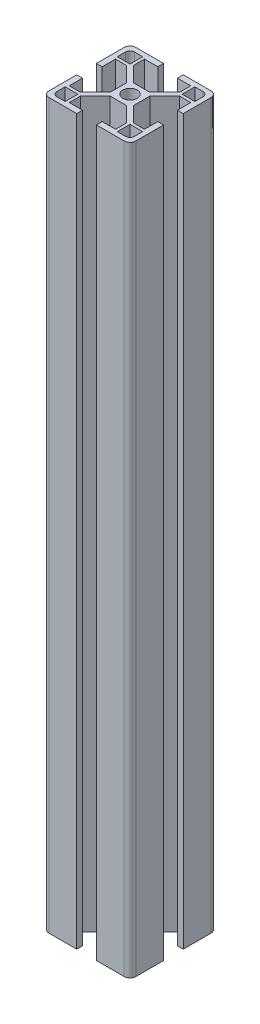
SolidWorks part; units mm, degrees
ref_plane "Front Plane" through (0, 0, 0) normal (0, 0, 1) x (1, 0, 0)
ref_plane "Top Plane" through (0, 0, 0) normal (0, 1, 0) x (1, 0, 0)
ref_plane "Right Plane" through (0, 0, 0) normal (1, 0, 0) x (0, 0, -1)
sketch "Sketch1" plane through (0, 0, 0) normal (0, 1, 0) x (1, 0, 0)
  line L0 (0, 15) -> (30, 15) construction
  line L1 (0, 28) -> (0, 18.4)
  line L2 (30, 28) -> (30, 18.4)
  line L3 (2, 30) -> (11.6, 30)
  line L4 (28, 30) -> (18.4, 30)
  line L5 (15, 0) -> (15, 30) construction
  line L6 (30, 0) -> (11, 19) construction
  line L7 (0, 0) -> (30, 30) construction
  line L8 (5.8333, 23) -> (11, 17.8333)
  line L9 (18.4, 28) -> (18.4, 30)
  line L10 (23, 28) -> (18.4, 28)
  line L11 (15, 19) -> (12.1667, 19)
  line L12 (11, 15) -> (11, 17.8333)
  line L13 (19, 11) -> (11, 19) construction
  line L14 (19, 19) -> (11, 11) construction
  line L15 (7, 24.1667) -> (12.1667, 19)
  line L16 (7, 28) -> (11.6, 28)
  line L17 (11.6, 28) -> (11.6, 30)
  line L18 (2, 23) -> (2, 18.4)
  line L19 (2, 18.4) -> (0, 18.4)
  line L20 (6, 28.4) -> (6, 24)
  line L21 (3.2, 28.4) -> (6, 28.4)
  line L22 (1.6, 26.8) -> (1.6, 24)
  line L23 (2, 23) -> (5.8333, 23)
  line L24 (7, 28) -> (7, 24.1667)
  line L25 (6, 24) -> (1.6, 24)
  line L26 (26.8, 28.4) -> (24, 28.4)
  line L27 (28.4, 26.8) -> (28.4, 24)
  line L28 (28, 23) -> (28, 18.4)
  line L29 (28, 18.4) -> (30, 18.4)
  line L30 (23, 28) -> (23, 24.1667)
  line L31 (24, 24) -> (24, 28.4)
  line L32 (28.4, 24) -> (24, 24)
  line L33 (28, 23) -> (24.1667, 23)
  line L34 (24.1667, 23) -> (19, 17.8333)
  line L35 (23, 24.1667) -> (17.8333, 19)
  line L36 (15, 19) -> (17.8333, 19)
  line L37 (19, 15) -> (19, 17.8333)
  line L38 (28, 0) -> (18.4, 0)
  line L39 (30, 2) -> (30, 11.6)
  line L40 (28, 11.6) -> (30, 11.6)
  line L41 (28, 7) -> (28, 11.6)
  line L42 (28.4, 3.2) -> (28.4, 6)
  line L43 (26.8, 1.6) -> (24, 1.6)
  line L44 (23, 2) -> (18.4, 2)
  line L45 (18.4, 2) -> (18.4, 0)
  line L46 (28, 7) -> (24.1667, 7)
  line L47 (24, 6) -> (28.4, 6)
  line L48 (24, 1.6) -> (24, 6)
  line L49 (23, 2) -> (23, 5.8333)
  line L50 (23, 5.8333) -> (17.8333, 11)
  line L51 (24.1667, 7) -> (19, 12.1667)
  line L52 (19, 15) -> (19, 12.1667)
  line L53 (15, 11) -> (17.8333, 11)
  line L54 (0, 2) -> (0, 11.6)
  line L55 (2, 0) -> (11.6, 0)
  line L56 (11.6, 2) -> (11.6, 0)
  line L57 (7, 2) -> (11.6, 2)
  line L58 (3.2, 1.6) -> (6, 1.6)
  line L59 (1.6, 3.2) -> (1.6, 6)
  line L60 (2, 7) -> (2, 11.6)
  line L61 (2, 11.6) -> (0, 11.6)
  line L62 (7, 2) -> (7, 5.8333)
  line L63 (6, 6) -> (6, 1.6)
  line L64 (1.6, 6) -> (6, 6)
  line L65 (2, 7) -> (5.8333, 7)
  line L66 (5.8333, 7) -> (11, 12.1667)
  line L67 (7, 5.8333) -> (12.1667, 11)
  line L68 (15, 11) -> (12.1667, 11)
  line L69 (11, 15) -> (11, 12.1667)
  arc A0 (15, 17.5) -> (12.5, 15) centre (15, 15) ccw
  arc A1 (3.2, 28.4) -> (1.6, 26.8) centre (3.2, 26.8) ccw
  arc A2 (0, 28) -> (2, 30) centre (2, 28) cw
  arc A3 (28, 30) -> (30, 28) centre (28, 28) cw
  arc A4 (28.4, 26.8) -> (26.8, 28.4) centre (26.8, 26.8) ccw
  arc A5 (17.5, 15) -> (15, 17.5) centre (15, 15) ccw
  arc A6 (30, 2) -> (28, 0) centre (28, 2) cw
  arc A7 (26.8, 1.6) -> (28.4, 3.2) centre (26.8, 3.2) ccw
  arc A8 (15, 12.5) -> (17.5, 15) centre (15, 15) ccw
  arc A9 (2, 0) -> (0, 2) centre (2, 2) cw
  arc A10 (1.6, 3.2) -> (3.2, 1.6) centre (3.2, 3.2) ccw
  arc A11 (12.5, 15) -> (15, 12.5) centre (15, 15) ccw
  point P10 (1.3411, 29.5046)
  point P109 (15, 15)
  dimension "D3" = 30
  dimension "D16" = 1.6
  dimension "D2" = 2
  dimension "D4" = 30
  dimension "D5" = 1.65
  dimension "D6" = 2
  dimension "D7" = 4
  dimension "D11" = 7
  dimension "D12" = 1.6
  dimension "D14" = 1
  dimension "D15" = 1
extrude "Boss-Extrude1" add sketch "Sketch1" along normal blind 250
